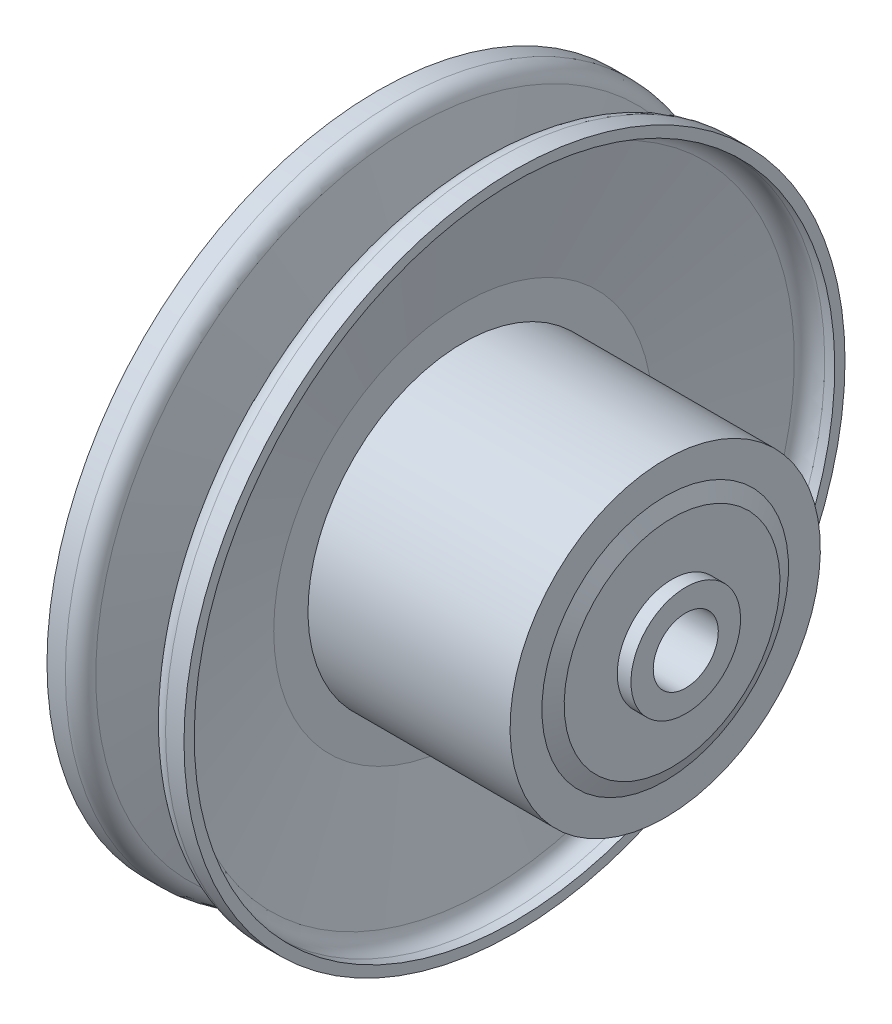
SolidWorks part; units mm, degrees
material "AISI 1020"
ref_plane "Спереди" through (0, 0, 0) normal (0, 0, 1) x (1, 0, 0)
ref_plane "Сверху" through (0, 0, 0) normal (0, 1, 0) x (1, 0, 0)
ref_plane "Справа" through (0, 0, 0) normal (1, 0, 0) x (0, 0, -1)
sketch "Эскиз1" plane through (0, 0, 0) normal (0, 0, 1) x (1, 0, 0)
  line L0 (-45, 0) -> (45, 0) construction
  line L1 (45, 9.5) -> (-40, 9.5)
  line L2 (45, 9.5) -> (45, 16)
  line L3 (45, 16) -> (41, 16)
  line L4 (41, 16) -> (41, 31.5)
  line L5 (41, 31.5) -> (39, 36)
  line L6 (39, 36) -> (39, 45.3)
  line L7 (39, 45.3) -> (-20, 45.3)
  line L8 (-20, 45.3) -> (-20, 55.3)
  line L9 (-20, 55.3) -> (-12, 93.5)
  line L10 (-12, 93.5) -> (-5, 93.5)
  line L11 (-5, 93.5) -> (-5, 96.5)
  line L12 (-5, 96.5) -> (-14.4368, 96.5)
  line L13 (-14.4368, 96.5) -> (-23, 55.6108)
  line L14 (-27, 55.6108) -> (-35.5632, 96.5)
  line L15 (-35.5632, 96.5) -> (-45, 96.5)
  line L16 (-45, 96.5) -> (-45, 93.5)
  line L17 (-45, 93.5) -> (-38, 93.5)
  line L18 (-38, 93.5) -> (-30, 55.3)
  line L19 (-23, 55.6108) -> (-23, 35)
  line L20 (-23, 35) -> (-27, 35)
  line L21 (-27, 35) -> (-27, 55.6108)
  line L23 (-35, 45.3) -> (-35, 14)
  line L24 (-35, 14) -> (-40, 14)
  line L25 (-40, 14) -> (-40, 9.5)
  line L26 (-30, 55.3) -> (-30, 45.3)
  line L27 (-30, 45.3) -> (-35, 45.3)
  point P2 (0, 0)
  point P28 (0, 0)
  dimension "D1" = 90
  dimension "D2" = 19
  dimension "D3" = 4
  dimension "D4" = 32
  dimension "D5" = 63
  dimension "D6" = 72
  dimension "D7" = 90.6
  dimension "D8" = 2
  dimension "D9" = 59
  dimension "D10" = 15
  dimension "D11" = 193
  dimension "D12" = 3
  dimension "D13" = 7
  dimension "D14" = 3
  dimension "D15" = 10
  dimension "D16" = 3
  dimension "D17" = 70
  dimension "D18" = 5
  dimension "D19" = 28
  dimension "D20" = 5
  dimension "D21" = 85
revolve "Повернуть1" add sketch "Эскиз1" angle 360 about L0
fillet "Скругление1" radius 5 4 edges at (-12, -93.5, 0) (-14.4368, -96.5, 0) (-38, -93.5, 0) (-35.5632, -96.5, 0)
sketch "Эскиз2" plane through (-40, 0, 0) normal (-1, 0, 0) x (0, 0, 1)
  line L0 (-997.8791, 9.5) -> (49002.1209, 9.5) construction
  line L1 (-2.5, 12) -> (2.5, 12)
  line L2 (-2.5, 12) -> (-2.5, 7)
  line L3 (-2.5, 7) -> (2.5, 7)
  line L4 (2.5, 12) -> (2.5, 7)
  circle A0 centre (0, 0) radius 9.5 construction
  point P4 (0, 7)
  point P9 (2.5, 9.5)
  dimension "D1" = 5
extrude "Бобышка-Вытянуть1" add sketch "Эскиз2" against normal offset from surface (35 mm away) 38 from offset 12 up to face at (45, -16, 0)
